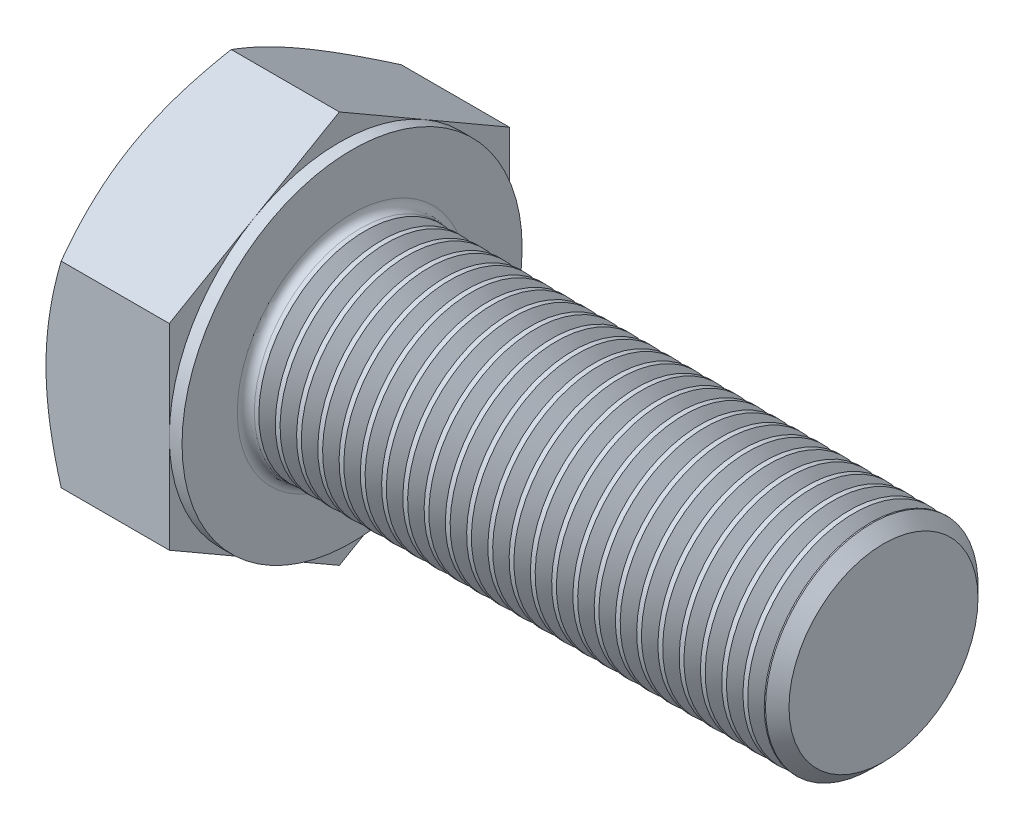
SolidWorks part; units mm, degrees
ref_plane "Plane1" through (0, 0, 0) normal (0, 0, 1) x (1, 0, 0)
ref_plane "Plane2" through (0, 0, 0) normal (0, 1, 0) x (1, 0, 0)
ref_plane "Plane3" through (0, 0, 0) normal (1, 0, 0) x (0, 0, -1)
sketch "Sketch1" plane through (0, 0, 0) normal (1, 0, 0) x (0, 0, -1)
  line L0 (8, 4.6188) -> (8, -4.6188)
  line L1 (-8, 4.6188) -> (-8, -4.6188)
  line L2 (8, -4.6188) -> (0, -9.2376)
  line L3 (0, -9.2376) -> (-8, -4.6188)
  line L4 (8, 4.6188) -> (0, 9.2376)
  line L5 (0, 9.2376) -> (-8, 4.6188)
  dimension "Width_flats" = 16
  dimension "D2" = 120
  dimension "D3" = 8
  dimension "D4" = 8
  dimension "D5" = 8
extrude "BaseHead" add sketch "Sketch1" along normal blind 6.4
sketch "BodySke" plane through (0, 0, 0) normal (0, 0, 1) x (1, 0, 0)
  line L0 (0, 4.6188) -> (0, -4.6188) construction
  line L1 (0, 0) -> (31.4, 0)
  line L2 (0, 0) -> (0, 5)
  line L3 (0, 5) -> (30.8455, 5)
  line L4 (31.4, 0) -> (31.4, 4.4455)
  line L5 (6.4, 9.2376) -> (6.4, 4.6188) construction
  line L6 (31.4, 4.4455) -> (30.8455, 5)
  line L7 (0, 0) -> (96.52, 0) construction
  line L8 (31.4, -4.4455) -> (30.8455, -5) construction
  line L9 (0, -5) -> (30.8455, -5) construction
  line L10 (7.4, 15.24) -> (7.4, -1.27) construction
  line L12 (6.4, 4.6188) -> (6.4, -4.6188) construction
  dimension "Length" = 25
  dimension "Body_ch_ang" = 45
  dimension "Diameter" = 10
  dimension "Minor_dia" = 8.891
  dimension "Advance" = 1
revolve "BaseBody" add sketch "BodySke"
cosmetic thread "ThreadCosmetic" [suppressed]
fillet "HeadFillet" radius 0.4 1 edges at (6.4, 0, -5)
sketch "Sketch3" plane through (0, 0, 0) normal (0, 0, 1) x (1, 0, 0)
  line L0 (0, 8) -> (3.6013, 14.2376)
  line L1 (0, 9.2376) -> (0, 4.6188) construction
  line L2 (3.6013, 14.2376) -> (3.6013, 19.2376)
  line L3 (3.6013, 19.2376) -> (-10, 19.2376)
  line L4 (-10, 19.2376) -> (-10, 8)
  line L5 (-10, 8) -> (0, 8)
  line L6 (0, 0) -> (99.06, 0) construction
  line L7 (6.4, 9.2376) -> (0, 9.2376) construction
  dimension "D1" = 8
  dimension "D2" = 5
  dimension "D3" = 10
  dimension "D4" = 5
  dimension "Head_ch_ang" = 30
revolve "HeadChamfer" cut sketch "Sketch3" angle 360 about L6
sketch "Sketch4" plane through (0, 0, 0) normal (0, 0, 1) x (1, 0, 0)
  line L1 (6.4, 9.2376) -> (6.4, 4.6188) construction
  line L2 (6.4, 8) -> (5.8, 8)
  line L3 (6.4, 8) -> (6.4, 19.2376)
  line L4 (6.4, 19.2376) -> (5.8, 19.2376)
  line L5 (0, 0) -> (95.25, 0) construction
  line L6 (0, 0) -> (96.52, 0) construction
  line L7 (5.8, 8) -> (5.8, 19.2376)
  line L8 (6.4, 9.2376) -> (0.7145, 9.2376) construction
  dimension "D1" = 16
  dimension "D2" = 10
  dimension "Bearing_ht" = 0.6
revolve "BearingFace" cut sketch "Sketch4" angle 360 about L5
sketch "ThdSchSke" plane through (0, 0, 0) normal (0, 0, 1) x (1, 0, 0)
  line L0 (7.4, -4.4455) -> (7.0117, -5)
  line L1 (7.4, -4.4455) -> (7.7883, -5)
  line L2 (7.7883, -5) -> (7.7883, -6.25)
  line L3 (-3.175, 0) -> (5.1513, 0) construction
  line L5 (7.7883, -6.25) -> (7.0117, -6.25)
  line L6 (7.0117, -6.25) -> (7.0117, -5)
  dimension "Thread_minor" = 8.891
  dimension "Diameter" = 10
  dimension "Start" = 7.4
  dimension "SideAngle" = 55
  dimension "VeeAngle" = 70
  dimension "Overcut" = 12.5
revolve "ThreadSchematic" cut sketch "ThdSchSke" angle 360 about L3
pattern_linear "ThdSchPat" count 24 spacing 1 along (1, 0, 0) of "ThreadSchematic"
equation "\"D3@Sketch1\" = \"Width_flats@Sketch1\" / 2"
equation "\"D4@Sketch1\" = \"D3@Sketch1\""
equation "\"D5@Sketch1\" = \"D4@Sketch1\""
equation "\"Thread_minor@ThreadCosmetic\" = \"Minor_dia@BodySke\""
equation "\"D1@Sketch3\" = \"Width_flats@Sketch1\" / 2"
equation "\"D1@Sketch4\" = \"Width_flats@Sketch1\""
equation "\"Thread_length@ThreadCosmetic\" = \"Length@BodySke\" - \"Advance@BodySke\""
equation "\"Thread_minor@ThdSchSke\" = \"Minor_dia@BodySke\""
equation "\"Diameter@ThdSchSke\" = \"Diameter@BodySke\""
equation "\"Overcut@ThdSchSke\" = \"Diameter@BodySke\" * 1.25"
equation "\"Start@ThdSchSke\" = \"Head_ht@BaseHead\" + \"Length@BodySke\" - \"Thread_length@ThreadCosmetic\"  '---Non-countersunk---"
equation "\"Num_threads@ThdSchPat\" = int( \"Thread_length@ThreadCosmetic\" / \"Advance@BodySke\" + 0.999 )  + 1"
equation "\"Advance@ThdSchPat\" = \"Thread_length@ThreadCosmetic\" /  (\"Num_threads@ThdSchPat\" - 1) 'relax it"
equation "\"Num_threads@ThdSchPat\" = \"Num_threads@ThdSchPat\" - sgn( \"Num_threads@ThdSchPat\" - 1) '---chamfered tips only---"
